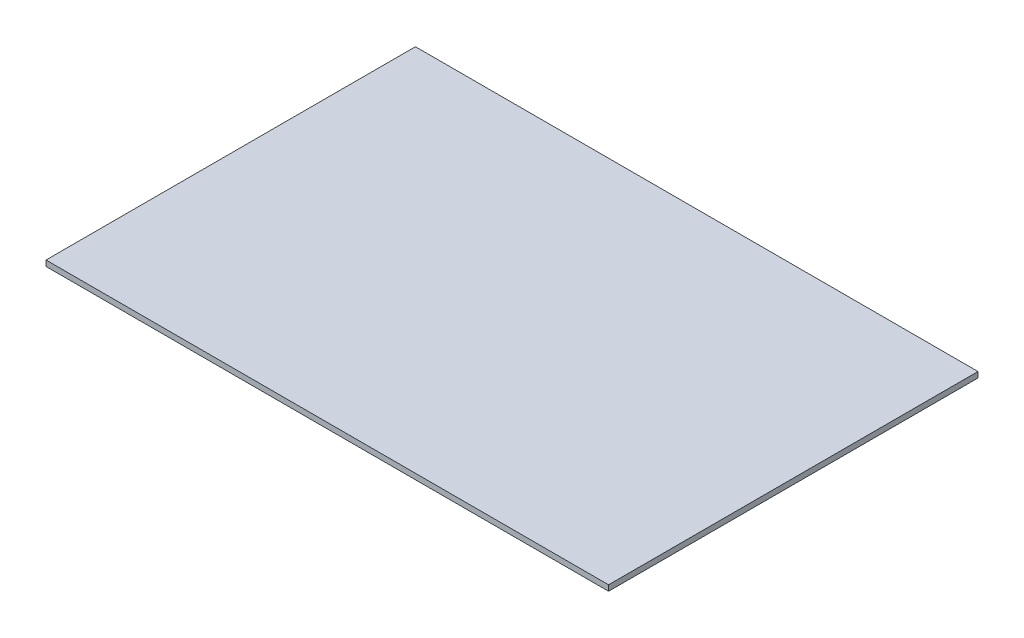
SolidWorks part; units mm, degrees
ref_plane "Front Plane" through (0, 0, 0) normal (0, 0, 1) x (1, 0, 0)
ref_plane "Top Plane" through (0, 0, 0) normal (0, 1, 0) x (1, 0, 0)
ref_plane "Right Plane" through (0, 0, 0) normal (1, 0, 0) x (0, 0, -1)
sketch "Sketch1" plane through (0, 0, 0) normal (0, 1, 0) x (1, 0, 0)
  line L1 (-150, -98.5) -> (150, -98.5)
  line L2 (-150, -98.5) -> (-150, 98.5)
  line L3 (-150, 98.5) -> (150, 98.5)
  line L4 (150, -98.5) -> (150, 98.5)
  line L5 (-150, -98.5) -> (150, 98.5) construction
  line L6 (-150, 98.5) -> (150, -98.5) construction
  point P0 (0, 0)
  dimension "D1" = 300
  dimension "D2" = 197
extrude "Boss-Extrude1" add sketch "Sketch1" along normal blind 3
